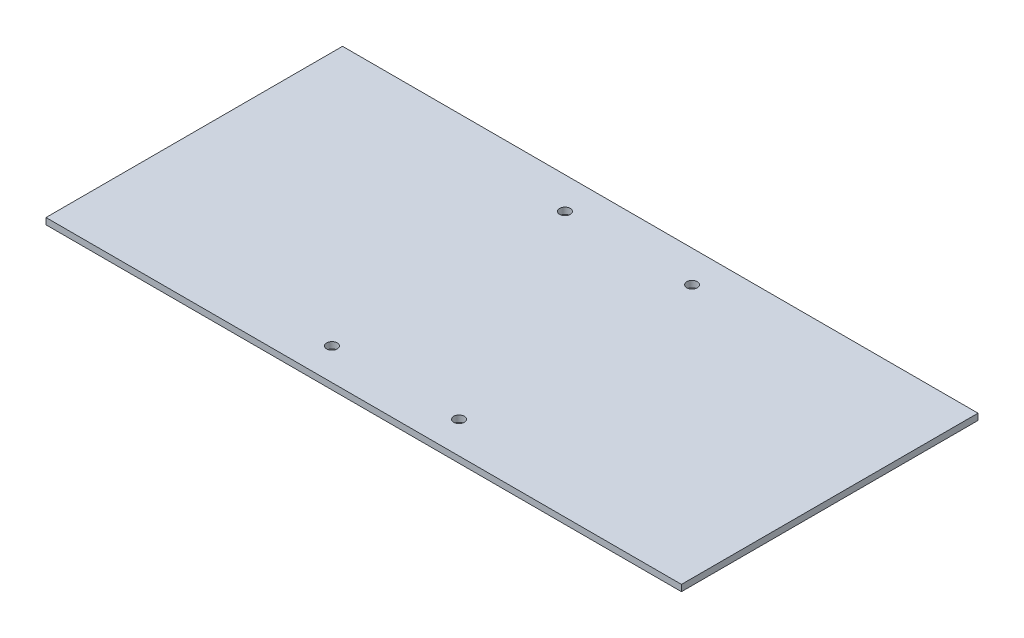
SolidWorks part; units mm, degrees
ref_plane "前视基准面" through (0, 0, 0) normal (0, 0, 1) x (1, 0, 0)
ref_plane "上视基准面" through (0, 0, 0) normal (0, 1, 0) x (1, 0, 0)
ref_plane "右视基准面" through (0, 0, 0) normal (1, 0, 0) x (0, 0, -1)
sketch "草图1" plane through (0, 0, 0) normal (0, 1, 0) x (1, 0, 0)
  line L1 (-150, 70) -> (150, 70)
  line L2 (-150, 70) -> (-150, -70)
  line L3 (-150, -70) -> (150, -70)
  line L4 (150, 70) -> (150, -70)
  point P7 (-1154.6535, 429.0099)
  point P8 (0, 0)
  point P9 (-362.1234, 190.5717)
  dimension "D1" = 70
  dimension "D2" = 70
  dimension "D3" = 150
  dimension "D4" = 150
extrude "凸台-拉伸1" add sketch "草图1" along normal blind 3
sketch "草图2" plane through (0, 3, 0) normal (0, 1, 0) x (1, 0, 0)
  line L0 (-150, 70) -> (-150, -70) construction
  line L2 (150, 70) -> (-150, 70) construction
  line L3 (150, -70) -> (150, 70) construction
  circle A0 centre (-30, 55) radius 2.5
  circle A1 centre (30, 55) radius 2.5
  point P12 (-61.2447, 95.1837)
  point P13 (0, 0)
  dimension "D1" = 5
  dimension "D4" = 5
  dimension "D2" = 120
  dimension "D3" = 15
  dimension "D5" = 120
  dimension "D6" = 15
extrude "切除-拉伸1" cut sketch "草图2" against normal blind 3
mirror "镜向1" about plane through (0, 0, 0) normal (0, 0, 1) of "切除-拉伸1"
